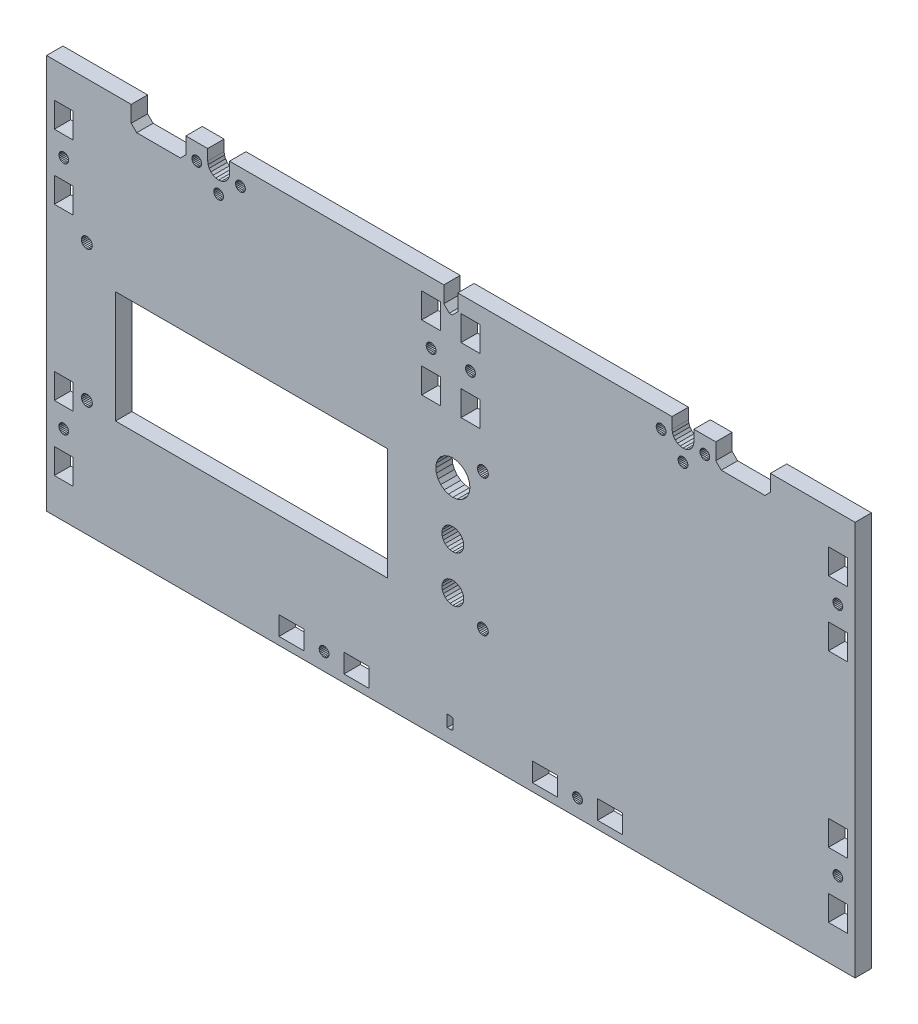
SolidWorks part; units mm, degrees
material "Maple"
ref_plane "Front Plane" through (0, 0, 0) normal (0, 0, 1) x (1, 0, 0)
ref_plane "Top Plane" through (0, 0, 0) normal (0, 1, 0) x (1, 0, 0)
ref_plane "Right Plane" through (0, 0, 0) normal (1, 0, 0) x (0, 0, -1)
sketch "Sketch1" plane through (0, 0, 0) normal (0, 0, 1) x (1, 0, 0)
  line L5557 (-18.0811, -260.3965) -> (-17.9448, -259.3613)
  line L5558 (-189.9448, -262.8254) -> (-189.1163, -262.1897)
  line L5559 (-21.9448, -263.3613) -> (-20.9095, -263.225)
  line L5560 (41.0552, -255.3613) -> (41.0552, -399.8612)
  line L5561 (-254.9447, -255.3613) -> (-223.9448, -255.3613)
  line L5562 (8.0552, -263.3613) -> (-7.9448, -263.3613)
  line L5563 (-9.9448, -255.3613) -> (-9.9448, -261.3613)
  line L5564 (-189.1163, -262.1897) -> (-188.4807, -261.3613)
  line L5565 (-19.1164, -262.1897) -> (-18.4807, -261.3613)
  line L5566 (-223.9448, -261.3613) -> (-223.9448, -255.3613)
  line L5567 (-20.9095, -263.225) -> (-19.9448, -262.8254)
  line L5568 (-25.9448, -259.3613) -> (-25.8085, -260.3965)
  line L5569 (-188.0811, -260.3965) -> (-187.9448, -259.3613)
  line L5570 (-203.9448, -255.3613) -> (-195.9448, -255.3613)
  line L5571 (-188.4807, -261.3613) -> (-188.0811, -260.3965)
  line L5572 (-223.9448, -261.3613) -> (-221.9448, -263.3613)
  line L5573 (-203.9448, -261.3613) -> (-203.9448, -255.3613)
  line L5574 (-193.9448, -262.8254) -> (-192.98, -263.225)
  line L5575 (10.0552, -255.3613) -> (10.0552, -261.3613)
  line L5576 (-187.9448, -255.3613) -> (-109.4948, -255.3613)
  line L5577 (-195.9448, -259.3613) -> (-195.8085, -260.3965)
  line L5578 (-17.9448, -259.3613) -> (-17.9448, -255.3613)
  line L5579 (-192.98, -263.225) -> (-191.9448, -263.3613)
  line L5580 (-205.9448, -263.3613) -> (-221.9448, -263.3613)
  line L5581 (-9.9448, -261.3613) -> (-7.9448, -263.3613)
  line L5582 (-17.9448, -255.3613) -> (-9.9448, -255.3613)
  line L5583 (-23.9448, -262.8254) -> (-22.9801, -263.225)
  line L5584 (-25.4089, -261.3613) -> (-24.7732, -262.1897)
  line L5585 (41.0552, -399.8612) -> (-254.9447, -399.8612)
  line L5586 (-18.4807, -261.3613) -> (-18.0811, -260.3965)
  line L5587 (-195.9448, -259.3613) -> (-195.9448, -255.3613)
  line L5588 (-195.8085, -260.3965) -> (-195.4089, -261.3613)
  line L5589 (-19.9448, -262.8254) -> (-19.1164, -262.1897)
  line L5590 (-254.9447, -399.8612) -> (-254.9447, -255.3613)
  line L5591 (10.0552, -261.3613) -> (8.0552, -263.3613)
  line L5592 (-25.8085, -260.3965) -> (-25.4089, -261.3613)
  line L5593 (-22.9801, -263.225) -> (-21.9448, -263.3613)
  line L5594 (-187.9448, -259.3613) -> (-187.9448, -255.3613)
  line L5595 (-191.9448, -263.3613) -> (-190.9095, -263.225)
  line L5596 (-195.4089, -261.3613) -> (-194.7732, -262.1897)
  line L5597 (-25.9448, -259.3613) -> (-25.9448, -255.3613)
  line L5598 (10.0552, -255.3613) -> (41.0552, -255.3613)
  line L5599 (-203.9448, -261.3613) -> (-205.9448, -263.3613)
  line L5600 (-190.9095, -263.225) -> (-189.9448, -262.8254)
  line L5601 (-24.7732, -262.1897) -> (-23.9448, -262.8254)
  line L5602 (-194.7732, -262.1897) -> (-193.9448, -262.8254)
  line L5603 (36.0292, -285.7853) -> (36.3155, -285.4121)
  line L5604 (-190.3859, -266.9613) -> (-190.672, -266.5885)
  line L5605 (-13.4801, -259.6226) -> (-13.9459, -259.5613)
  line L5606 (-185.6846, -260.8954) -> (-185.7459, -261.3613)
  line L5607 (38.2052, -268.0113) -> (31.3052, -268.0113)
  line L5608 (-252.0947, -301.1113) -> (-245.1947, -301.1113)
  line L5609 (-190.3859, -268.7613) -> (-190.2061, -268.3271)
  line L5610 (35.656, -282.9509) -> (35.2215, -282.7709)
  line L5611 (-198.1448, -261.3613) -> (-198.2061, -260.8954)
  line L5612 (33.4811, -283.2372) -> (33.1948, -283.6104)
  line L5613 (-59.2708, -394.8353) -> (-58.9845, -394.4621)
  line L5614 (-62.3465, -393.5613) -> (-62.2851, -394.0276)
  line L5615 (-30.8448, -262.9201) -> (-30.4107, -263.0999)
  line L5616 (-30.4107, -259.6226) -> (-30.8448, -259.8024)
  line L5617 (-185.2187, -260.0885) -> (-185.5047, -260.4613)
  line L5618 (-198.3859, -260.4613) -> (-198.672, -260.0885)
  line L5619 (-182.2072, -260.8954) -> (-182.387, -260.4613)
  line L5620 (-252.0947, -268.1113) -> (-252.0947, -277.3113)
  line L5621 (-31.7448, -261.3613) -> (-31.6835, -261.8271)
  line L5622 (-67.8448, -397.0113) -> (-67.8448, -390.1112)
  line L5623 (-154.9051, -394.4621) -> (-154.6188, -394.8353)
  line L5624 (-192.4106, -269.5999) -> (-191.9448, -269.6613)
  line L5625 (-246.9044, -285.0776) -> (-246.843, -284.6113)
  line L5626 (-160.6448, -390.1112) -> (-169.8448, -390.1112)
  line L5627 (-247.7439, -286.1716) -> (-247.3707, -285.8853)
  line L5628 (-192.4106, -266.1226) -> (-192.8448, -266.3024)
  line L5629 (31.3052, -301.0113) -> (38.2052, -301.0113)
  line L5630 (-136.8448, -397.0113) -> (-136.8448, -390.1112)
  line L5631 (-23.2176, -269.1341) -> (-22.8448, -269.4201)
  line L5632 (-183.9459, -263.1613) -> (-183.48, -263.0999)
  line L5633 (-252.0947, -291.9113) -> (-252.0947, -301.1113)
  line L5634 (-155.0851, -393.0949) -> (-155.1465, -393.5613)
  line L5635 (-250.3851, -285.0776) -> (-250.2051, -285.5121)
  line L5636 (-183.9459, -259.5613) -> (-184.4118, -259.6226)
  line L5637 (33.0148, -284.0449) -> (32.9534, -284.5113)
  line L5638 (-182.6731, -260.0885) -> (-183.0459, -259.8024)
  line L5639 (-15.6846, -260.8954) -> (-15.7459, -261.3613)
  line L5640 (-247.0844, -283.7104) -> (-247.3707, -283.3372)
  line L5641 (-29.0448, -262.9201) -> (-28.672, -262.6341)
  line L5642 (-29.4789, -259.6226) -> (-29.9448, -259.5613)
  line L5643 (-146.0448, -390.1112) -> (-146.0448, -397.0113)
  line L5644 (-61.8188, -392.2872) -> (-62.1052, -392.6604)
  line L5645 (-61.0111, -395.3016) -> (-60.5448, -395.363)
  line L5646 (-61.4457, -395.1216) -> (-61.0111, -395.3016)
  line L5647 (-250.2051, -285.5121) -> (-249.9188, -285.8853)
  line L5648 (-20.2062, -268.3271) -> (-20.1448, -267.8613)
  line L5649 (-193.6834, -267.3954) -> (-193.7448, -267.8613)
  line L5650 (-249.9188, -285.8853) -> (-249.5456, -286.1716)
  line L5651 (-28.2062, -261.8271) -> (-28.1448, -261.3613)
  line L5652 (-151.7844, -392.6604) -> (-152.0708, -392.2872)
  line L5653 (-199.9448, -259.5613) -> (-200.4106, -259.6226)
  line L5654 (-12.6731, -262.6341) -> (-12.3871, -262.2613)
  line L5655 (-31.2176, -262.6341) -> (-30.8448, -262.9201)
  line L5656 (-191.0448, -266.3024) -> (-191.4789, -266.1226)
  line L5657 (-199.9448, -263.1613) -> (-199.4789, -263.0999)
  line L5658 (31.3052, -268.0113) -> (31.3052, -277.2113)
  line L5659 (-190.672, -266.5885) -> (-191.0448, -266.3024)
  line L5660 (-152.4439, -395.1216) -> (-152.0708, -394.8353)
  line L5661 (-15.5048, -262.2613) -> (-15.2187, -262.6341)
  line L5662 (-12.3871, -260.4613) -> (-12.6731, -260.0885)
  line L5663 (-28.672, -262.6341) -> (-28.386, -262.2613)
  line L5664 (-20.386, -266.9613) -> (-20.672, -266.5885)
  line L5665 (-252.0947, -277.3113) -> (-245.1947, -277.3113)
  line L5666 (-23.5037, -266.9613) -> (-23.6835, -267.3954)
  line L5667 (32.9534, -284.5113) -> (33.0148, -284.9776)
  line L5668 (-182.387, -262.2613) -> (-182.2072, -261.8271)
  line L5669 (-201.2176, -262.6341) -> (-200.8448, -262.9201)
  line L5670 (-20.672, -269.1341) -> (-20.386, -268.7613)
  line L5671 (-136.8448, -390.1112) -> (-146.0448, -390.1112)
  line L5672 (-151.7844, -394.4621) -> (-151.6044, -394.0276)
  line L5673 (-20.672, -266.5885) -> (-21.0448, -266.3024)
  line L5674 (-14.8459, -259.8024) -> (-15.2187, -260.0885)
  line L5675 (-198.672, -260.0885) -> (-199.0448, -259.8024)
  line L5676 (-13.4801, -263.0999) -> (-13.0459, -262.9201)
  line L5677 (36.4955, -284.9776) -> (36.5569, -284.5113)
  line L5678 (33.0148, -284.9776) -> (33.1948, -285.4121)
  line L5679 (-23.5037, -268.7613) -> (-23.2176, -269.1341)
  line L5680 (-151.6044, -394.0276) -> (-151.5431, -393.5613)
  line L5681 (-185.5047, -262.2613) -> (-185.2187, -262.6341)
  line L5682 (-183.0459, -262.9201) -> (-182.6731, -262.6341)
  line L5683 (-146.0448, -397.0113) -> (-136.8448, -397.0113)
  line L5684 (-192.8448, -269.4201) -> (-192.4106, -269.5999)
  line L5685 (33.8543, -286.0716) -> (34.2888, -286.2516)
  line L5686 (34.7552, -282.7095) -> (34.2888, -282.7709)
  line L5687 (-191.9448, -266.0613) -> (-192.4106, -266.1226)
  line L5688 (-14.4118, -263.0999) -> (-13.9459, -263.1613)
  line L5689 (-184.8459, -259.8024) -> (-185.2187, -260.0885)
  line L5690 (-21.9448, -266.0613) -> (-22.4107, -266.1226)
  line L5691 (-21.9448, -269.6613) -> (-21.4789, -269.5999)
  line L5692 (-22.8448, -269.4201) -> (-22.4107, -269.5999)
  line L5693 (-23.7448, -267.8613) -> (-23.6835, -268.3271)
  line L5694 (-22.8448, -266.3024) -> (-23.2176, -266.5885)
  line L5695 (-200.4106, -263.0999) -> (-199.9448, -263.1613)
  line L5696 (-154.6188, -394.8353) -> (-154.2456, -395.1216)
  line L5697 (-153.3448, -391.7595) -> (-153.8111, -391.8209)
  line L5698 (-152.8785, -391.8209) -> (-153.3448, -391.7595)
  line L5699 (-152.0708, -392.2872) -> (-152.4439, -392.0009)
  line L5700 (-60.0785, -395.3016) -> (-59.644, -395.1216)
  line L5701 (-62.2851, -394.0276) -> (-62.1052, -394.4621)
  line L5702 (-61.0111, -391.8209) -> (-61.4457, -392.0009)
  line L5703 (-29.0448, -259.8024) -> (-29.4789, -259.6226)
  line L5704 (-249.1111, -282.8709) -> (-249.5456, -283.0509)
  line L5705 (36.3155, -369.7104) -> (36.0292, -369.3372)
  line L5706 (33.1948, -371.5121) -> (33.4811, -371.8853)
  line L5707 (31.3052, -363.3113) -> (38.2052, -363.3113)
  line L5708 (36.0292, -371.8853) -> (36.3155, -371.5121)
  line L5709 (34.7552, -368.8095) -> (34.2888, -368.8709)
  line L5710 (35.656, -372.1716) -> (36.0292, -371.8853)
  line L5711 (35.656, -369.0509) -> (35.2215, -368.8709)
  line L5712 (36.5569, -370.6113) -> (36.4955, -370.1449)
  line L5713 (34.2888, -368.8709) -> (33.8543, -369.0509)
  line L5714 (36.3155, -371.5121) -> (36.4955, -371.0776)
  line L5715 (38.2052, -377.9113) -> (31.3052, -377.9113)
  line L5716 (32.9534, -370.6113) -> (33.0148, -371.0776)
  line L5717 (35.2215, -372.3516) -> (35.656, -372.1716)
  line L5718 (34.2888, -372.3516) -> (34.7552, -372.413)
  line L5719 (-249.5456, -372.1716) -> (-249.1111, -372.3516)
  line L5720 (-247.7439, -369.0509) -> (-248.1784, -368.8709)
  line L5721 (-245.1947, -354.1113) -> (-252.0947, -354.1113)
  line L5722 (-250.3851, -371.0776) -> (-250.2051, -371.5121)
  line L5723 (-249.5456, -369.0509) -> (-249.9188, -369.3372)
  line L5724 (-250.4465, -370.6113) -> (-250.3851, -371.0776)
  line L5725 (-247.3707, -371.8853) -> (-247.0844, -371.5121)
  line L5726 (-247.0844, -371.5121) -> (-246.9044, -371.0776)
  line L5727 (-246.9044, -370.1449) -> (-247.0844, -369.7104)
  line L5728 (-246.9044, -371.0776) -> (-246.843, -370.6113)
  line L5729 (-248.1784, -368.8709) -> (-248.6447, -368.8095)
  line L5730 (-249.9188, -371.8853) -> (-249.5456, -372.1716)
  line L5731 (-250.2051, -371.5121) -> (-249.9188, -371.8853)
  line L5732 (-249.1111, -372.3516) -> (-248.6447, -372.413)
  line L5733 (-252.0947, -387.1112) -> (-245.1947, -387.1112)
  line L5734 (-247.7439, -372.1716) -> (-247.3707, -371.8853)
  line L5735 (-102.3378, -333.3081) -> (-102.7374, -332.3433)
  line L5736 (-110.0652, -333.3081) -> (-110.2015, -334.3433)
  line L5737 (-108.2015, -330.8792) -> (-109.0299, -331.5149)
  line L5738 (-109.6656, -353.3433) -> (-109.0299, -354.1718)
  line L5739 (-107.2367, -330.4796) -> (-108.2015, -330.8792)
  line L5740 (-110.2015, -351.3433) -> (-110.0652, -352.3786)
  line L5741 (-109.6656, -332.3433) -> (-110.0652, -333.3081)
  line L5742 (-103.0765, -309.4307) -> (-104.5838, -308.8063)
  line L5743 (-110.6209, -319.2627) -> (-109.3265, -320.256)
  line L5744 (-102.3378, -350.308) -> (-102.7374, -349.3433)
  line L5745 (-102.2015, -351.3433) -> (-102.3378, -350.308)
  line L5746 (-112.4515, -314.8433) -> (-112.2385, -316.4609)
  line L5747 (-104.2015, -354.8074) -> (-103.373, -354.1718)
  line L5748 (-109.3265, -309.4307) -> (-110.6209, -310.4239)
  line L5749 (-107.2367, -355.207) -> (-106.2015, -355.3433)
  line L5750 (-99.9515, -314.8433) -> (-100.1644, -313.2257)
  line L5751 (-104.2015, -330.8792) -> (-105.1662, -330.4796)
  line L5752 (-102.3378, -335.3786) -> (-102.2015, -334.3433)
  line L5753 (-111.6141, -311.7183) -> (-112.2385, -313.2257)
  line L5754 (-109.6656, -336.3433) -> (-109.0299, -337.1718)
  line L5755 (-112.2385, -313.2257) -> (-112.4515, -314.8433)
  line L5756 (-110.0652, -350.308) -> (-110.2015, -351.3433)
  line L5757 (-229.7014, -358.6433) -> (-130.2015, -358.6433)
  line L5758 (-108.2015, -337.8074) -> (-107.2367, -338.207)
  line L5759 (-101.782, -319.2627) -> (-100.7888, -317.9683)
  line L5760 (-107.8191, -308.8063) -> (-109.3265, -309.4307)
  line L5761 (-229.7014, -317.6433) -> (-229.7014, -358.6433)
  line L5762 (-106.2015, -355.3433) -> (-105.1662, -355.207)
  line L5763 (-109.6656, -349.3433) -> (-110.0652, -350.308)
  line L5764 (-102.7374, -336.3433) -> (-102.3378, -335.3786)
  line L5765 (-103.373, -337.1718) -> (-102.7374, -336.3433)
  line L5766 (-107.2367, -338.207) -> (-106.2015, -338.3433)
  line L5767 (33.1948, -369.7104) -> (33.0148, -370.1449)
  line L5768 (-14.8459, -262.9201) -> (-14.4118, -263.0999)
  line L5769 (-28.1448, -261.3613) -> (-28.2062, -260.8954)
  line L5770 (33.8543, -372.1716) -> (34.2888, -372.3516)
  line L5771 (-108.2015, -354.8074) -> (-107.2367, -355.207)
  line L5772 (-112.2385, -316.4609) -> (-111.6141, -317.9683)
  line L5773 (-152.4439, -392.0009) -> (-152.8785, -391.8209)
  line L5774 (38.2052, -387.1112) -> (38.2052, -377.9113)
  line L5775 (-250.3851, -284.1449) -> (-250.4465, -284.6113)
  line L5776 (-247.0844, -369.7104) -> (-247.3707, -369.3372)
  line L5777 (-200.4106, -259.6226) -> (-200.8448, -259.8024)
  line L5778 (-100.7888, -317.9683) -> (-100.1644, -316.4609)
  line L5779 (-106.2203, -394.8434) -> (-106.1594, -394.7541)
  line L5780 (-106.1594, -394.7541) -> (-106.1391, -394.6577)
  line L5781 (-199.0448, -262.9201) -> (-198.672, -262.6341)
  line L5782 (-110.2015, -334.3433) -> (-110.0652, -335.3786)
  line L5783 (-109.3265, -320.256) -> (-107.8191, -320.8804)
  line L5784 (33.1948, -285.4121) -> (33.4811, -285.7853)
  line L5785 (-193.2176, -266.5885) -> (-193.5036, -266.9613)
  line L5786 (-190.672, -269.1341) -> (-190.3859, -268.7613)
  line L5787 (-155.1465, -393.5613) -> (-155.0851, -394.0276)
  line L5788 (34.7552, -372.413) -> (35.2215, -372.3516)
  line L5789 (31.3052, -277.2113) -> (38.2052, -277.2113)
  line L5790 (-67.8448, -390.1112) -> (-77.0448, -390.1112)
  line L5791 (-21.0448, -269.4201) -> (-20.672, -269.1341)
  line L5792 (-20.1448, -267.8613) -> (-20.2062, -267.3954)
  line L5793 (-103.373, -348.5149) -> (-104.2015, -347.8792)
  line L5794 (-31.2176, -260.0885) -> (-31.5037, -260.4613)
  line L5795 (-23.6835, -268.3271) -> (-23.5037, -268.7613)
  line L5796 (-106.2015, -347.3433) -> (-107.2367, -347.4796)
  line L5797 (36.3155, -283.6104) -> (36.0292, -283.2372)
  line L5798 (35.2215, -286.2516) -> (35.656, -286.0716)
  line L5799 (-248.6447, -372.413) -> (-248.1784, -372.3516)
  line L5800 (-31.5037, -262.2613) -> (-31.2176, -262.6341)
  line L5801 (-106.8291, -390.8664) -> (-107.263, -390.8305)
  line L5802 (-105.1662, -347.4796) -> (-106.2015, -347.3433)
  line L5803 (-183.48, -263.0999) -> (-183.0459, -262.9201)
  line L5804 (-193.7448, -267.8613) -> (-193.6834, -268.3271)
  line L5805 (-59.644, -395.1216) -> (-59.2708, -394.8353)
  line L5806 (-152.0708, -394.8353) -> (-151.7844, -394.4621)
  line L5807 (34.2888, -286.2516) -> (34.7552, -286.313)
  line L5808 (-62.2851, -393.0949) -> (-62.3465, -393.5613)
  line L5809 (-250.4465, -284.6113) -> (-250.3851, -285.0776)
  line L5810 (33.4811, -371.8853) -> (33.8543, -372.1716)
  line L5811 (-247.3707, -283.3372) -> (-247.7439, -283.0509)
  line L5812 (-153.8111, -391.8209) -> (-154.2456, -392.0009)
  line L5813 (-44.0448, -397.0113) -> (-44.0448, -390.1112)
  line L5814 (31.3052, -377.9113) -> (31.3052, -387.1112)
  line L5815 (-185.5047, -260.4613) -> (-185.6846, -260.8954)
  line L5816 (36.4955, -284.0449) -> (36.3155, -283.6104)
  line L5817 (-246.843, -284.6113) -> (-246.9044, -284.1449)
  line L5818 (38.2052, -277.2113) -> (38.2052, -268.0113)
  line L5819 (-28.386, -260.4613) -> (-28.672, -260.0885)
  line L5820 (-182.387, -260.4613) -> (-182.6731, -260.0885)
  line L5821 (-60.5448, -395.363) -> (-60.0785, -395.3016)
  line L5822 (-106.1594, -391.2176) -> (-106.2203, -391.1302)
  line L5823 (-183.0459, -259.8024) -> (-183.48, -259.6226)
  line L5824 (-44.0448, -390.1112) -> (-53.2448, -390.1112)
  line L5825 (-245.1947, -363.3113) -> (-245.1947, -354.1113)
  line L5826 (-23.6835, -267.3954) -> (-23.7448, -267.8613)
  line L5827 (-106.2015, -308.5933) -> (-107.8191, -308.8063)
  line L5828 (-151.6044, -393.0949) -> (-151.7844, -392.6604)
  line L5829 (-30.4107, -263.0999) -> (-29.9448, -263.1613)
  line L5830 (-106.2015, -321.0933) -> (-104.5838, -320.8804)
  line L5831 (-22.4107, -269.5999) -> (-21.9448, -269.6613)
  line L5832 (-153.8111, -395.3016) -> (-153.3448, -395.363)
  line L5833 (36.5569, -284.5113) -> (36.4955, -284.0449)
  line L5834 (-252.0947, -377.9113) -> (-252.0947, -387.1112)
  line L5835 (-101.782, -310.4239) -> (-103.0765, -309.4307)
  line L5836 (-29.4789, -263.0999) -> (-29.0448, -262.9201)
  line L5837 (-110.0652, -335.3786) -> (-109.6656, -336.3433)
  line L5838 (-29.9448, -263.1613) -> (-29.4789, -263.0999)
  line L5839 (-15.6846, -261.8271) -> (-15.5048, -262.2613)
  line L5840 (-182.2072, -261.8271) -> (-182.1459, -261.3613)
  line L5841 (38.2052, -354.1113) -> (31.3052, -354.1113)
  line L5842 (-198.2061, -260.8954) -> (-198.3859, -260.4613)
  line L5843 (-252.0947, -354.1113) -> (-252.0947, -363.3113)
  line L5844 (-13.0459, -259.8024) -> (-13.4801, -259.6226)
  line L5845 (-191.9448, -269.6613) -> (-191.4789, -269.5999)
  line L5846 (-108.2808, -390.8305) -> (-107.263, -390.8305)
  line L5847 (-250.3851, -370.1449) -> (-250.4465, -370.6113)
  line L5848 (-185.2187, -262.6341) -> (-184.8459, -262.9201)
  line L5849 (-246.843, -370.6113) -> (-246.9044, -370.1449)
  line L5850 (-77.0448, -390.1112) -> (-77.0448, -397.0113)
  line L5851 (-199.0448, -259.8024) -> (-199.4789, -259.6226)
  line L5852 (-20.2062, -267.3954) -> (-20.386, -266.9613)
  line L5853 (-102.2015, -334.3433) -> (-102.3378, -333.3081)
  line L5854 (-182.1459, -261.3613) -> (-182.2072, -260.8954)
  line L5855 (-106.2015, -338.3433) -> (-105.1662, -338.207)
  line L5856 (36.4955, -371.0776) -> (36.5569, -370.6113)
  line L5857 (35.656, -286.0716) -> (36.0292, -285.7853)
  line L5858 (38.2052, -291.8113) -> (31.3052, -291.8113)
  line L5859 (-104.2015, -337.8074) -> (-103.373, -337.1718)
  line L5860 (-31.6835, -261.8271) -> (-31.5037, -262.2613)
  line L5861 (33.4811, -285.7853) -> (33.8543, -286.0716)
  line L5862 (-193.2176, -269.1341) -> (-192.8448, -269.4201)
  line L5863 (-248.1784, -282.8709) -> (-248.6447, -282.8095)
  line L5864 (-31.6835, -260.8954) -> (-31.7448, -261.3613)
  line L5865 (33.8543, -369.0509) -> (33.4811, -369.3372)
  line L5866 (-247.3707, -369.3372) -> (-247.7439, -369.0509)
  line L5867 (-249.1111, -286.3516) -> (-248.6447, -286.413)
  line L5868 (-198.3859, -262.2613) -> (-198.2061, -261.8271)
  line L5869 (-13.9459, -263.1613) -> (-13.4801, -263.0999)
  line L5870 (-248.6447, -282.8095) -> (-249.1111, -282.8709)
  line L5871 (-200.8448, -259.8024) -> (-201.2176, -260.0885)
  line L5872 (-154.2456, -395.1216) -> (-153.8111, -395.3016)
  line L5873 (-169.8448, -397.0113) -> (-160.6448, -397.0113)
  line L5874 (-248.1784, -286.3516) -> (-247.7439, -286.1716)
  line L5875 (-12.2073, -261.8271) -> (-12.1459, -261.3613)
  line L5876 (-153.3448, -395.363) -> (-152.8785, -395.3016)
  line L5877 (-190.2061, -268.3271) -> (-190.1448, -267.8613)
  line L5878 (-58.9845, -392.6604) -> (-59.2708, -392.2872)
  line L5879 (-61.4457, -392.0009) -> (-61.8188, -392.2872)
  line L5880 (-193.5036, -268.7613) -> (-193.2176, -269.1341)
  line L5881 (31.3052, -354.1113) -> (31.3052, -363.3113)
  line L5882 (-248.6447, -368.8095) -> (-249.1111, -368.8709)
  line L5883 (-201.2176, -260.0885) -> (-201.5036, -260.4613)
  line L5884 (-100.7888, -311.7183) -> (-101.782, -310.4239)
  line L5885 (-60.5448, -391.7595) -> (-61.0111, -391.8209)
  line L5886 (-102.7374, -332.3433) -> (-103.373, -331.5149)
  line L5887 (-15.5048, -260.4613) -> (-15.6846, -260.8954)
  line L5888 (-105.1662, -338.207) -> (-104.2015, -337.8074)
  line L5889 (33.4811, -369.3372) -> (33.1948, -369.7104)
  line L5890 (35.2215, -282.7709) -> (34.7552, -282.7095)
  line L5891 (-250.2051, -369.7104) -> (-250.3851, -370.1449)
  line L5892 (-15.2187, -262.6341) -> (-14.8459, -262.9201)
  line L5893 (-184.4118, -263.0999) -> (-183.9459, -263.1613)
  line L5894 (-201.5036, -262.2613) -> (-201.2176, -262.6341)
  line L5895 (-245.1947, -301.1113) -> (-245.1947, -291.9113)
  line L5896 (-58.8045, -393.0949) -> (-58.9845, -392.6604)
  line L5897 (-185.7459, -261.3613) -> (-185.6846, -261.8271)
  line L5898 (-249.5456, -286.1716) -> (-249.1111, -286.3516)
  line L5899 (-154.2456, -392.0009) -> (-154.6188, -392.2872)
  line L5900 (-201.6834, -261.8271) -> (-201.5036, -262.2613)
  line L5901 (-28.386, -262.2613) -> (-28.2062, -261.8271)
  line L5902 (-152.8785, -395.3016) -> (-152.4439, -395.1216)
  line L5903 (-245.1947, -291.9113) -> (-252.0947, -291.9113)
  line L5904 (-12.6731, -260.0885) -> (-13.0459, -259.8024)
  line L5905 (-249.9188, -283.3372) -> (-250.2051, -283.7104)
  line L5906 (-53.2448, -390.1112) -> (-53.2448, -397.0113)
  line L5907 (-109.0299, -348.5149) -> (-109.6656, -349.3433)
  line L5908 (-106.4638, -395.0011) -> (-106.8197, -395.1041)
  line L5909 (-106.8197, -395.1041) -> (-107.263, -395.1384)
  line L5910 (-109.0299, -354.1718) -> (-108.2015, -354.8074)
  line L5911 (-182.6731, -262.6341) -> (-182.387, -262.2613)
  line L5912 (-104.5838, -308.8063) -> (-106.2015, -308.5933)
  line L5913 (36.3155, -285.4121) -> (36.4955, -284.9776)
  line L5914 (-102.7374, -353.3433) -> (-102.3378, -352.3786)
  line L5915 (-12.1459, -261.3613) -> (-12.2073, -260.8954)
  line L5916 (-58.8045, -394.0276) -> (-58.7431, -393.5613)
  line L5917 (-245.1947, -277.3113) -> (-245.1947, -268.1113)
  line L5918 (-13.0459, -262.9201) -> (-12.6731, -262.6341)
  line L5919 (-23.2176, -266.5885) -> (-23.5037, -266.9613)
  line L5920 (-100.1644, -316.4609) -> (-99.9515, -314.8433)
  line L5921 (-169.8448, -390.1112) -> (-169.8448, -397.0113)
  line L5922 (-53.2448, -397.0113) -> (-44.0448, -397.0113)
  line L5923 (-12.3871, -262.2613) -> (-12.2073, -261.8271)
  line L5924 (-245.1947, -387.1112) -> (-245.1947, -377.9113)
  line L5925 (-59.644, -392.0009) -> (-60.0785, -391.8209)
  line L5926 (-191.0448, -269.4201) -> (-190.672, -269.1341)
  line L5927 (-201.6834, -260.8954) -> (-201.7448, -261.3613)
  line L5928 (-107.8191, -320.8804) -> (-106.2015, -321.0933)
  line L5929 (-245.1947, -377.9113) -> (-252.0947, -377.9113)
  line L5930 (-247.7439, -283.0509) -> (-248.1784, -282.8709)
  line L5931 (33.8543, -282.9509) -> (33.4811, -283.2372)
  line L5932 (-110.0652, -352.3786) -> (-109.6656, -353.3433)
  line L5933 (-106.2015, -330.3433) -> (-107.2367, -330.4796)
  line L5934 (38.2052, -301.0113) -> (38.2052, -291.8113)
  line L5935 (-15.7459, -261.3613) -> (-15.6846, -261.8271)
  line L5936 (-190.2061, -267.3954) -> (-190.3859, -266.9613)
  line L5937 (-28.672, -260.0885) -> (-29.0448, -259.8024)
  line L5938 (33.0148, -370.1449) -> (32.9534, -370.6113)
  line L5939 (-103.373, -331.5149) -> (-104.2015, -330.8792)
  line L5940 (-247.3707, -285.8853) -> (-247.0844, -285.5121)
  line L5941 (-200.8448, -262.9201) -> (-200.4106, -263.0999)
  line L5942 (-252.0947, -363.3113) -> (-245.1947, -363.3113)
  line L5943 (-106.1391, -391.3113) -> (-106.1391, -394.6577)
  line L5944 (-29.9448, -259.5613) -> (-30.4107, -259.6226)
  line L5945 (-62.1052, -392.6604) -> (-62.2851, -393.0949)
  line L5946 (-14.4118, -259.6226) -> (-14.8459, -259.8024)
  line L5947 (-102.7374, -349.3433) -> (-103.373, -348.5149)
  line L5948 (-21.4789, -266.1226) -> (-21.9448, -266.0613)
  line L5949 (-109.0299, -331.5149) -> (-109.6656, -332.3433)
  line L5950 (34.2888, -282.7709) -> (33.8543, -282.9509)
  line L5951 (-22.4107, -266.1226) -> (-22.8448, -266.3024)
  line L5952 (-21.0448, -266.3024) -> (-21.4789, -266.1226)
  line L5953 (-201.7448, -261.3613) -> (-201.6834, -261.8271)
  line L5954 (36.4955, -370.1449) -> (36.3155, -369.7104)
  line L5955 (-21.4789, -269.5999) -> (-21.0448, -269.4201)
  line L5956 (-12.2073, -260.8954) -> (-12.3871, -260.4613)
  line L5957 (31.3052, -291.8113) -> (31.3052, -301.0113)
  line L5958 (-198.2061, -261.8271) -> (-198.1448, -261.3613)
  line L5959 (34.7552, -286.313) -> (35.2215, -286.2516)
  line L5960 (-103.0765, -320.256) -> (-101.782, -319.2627)
  line L5961 (-184.4118, -259.6226) -> (-184.8459, -259.8024)
  line L5962 (-249.9188, -369.3372) -> (-250.2051, -369.7104)
  line L5963 (-249.5456, -283.0509) -> (-249.9188, -283.3372)
  line L5964 (-246.9044, -284.1449) -> (-247.0844, -283.7104)
  line L5965 (-104.2015, -347.8792) -> (-105.1662, -347.4796)
  line L5966 (-154.6188, -392.2872) -> (-154.9051, -392.6604)
  line L5967 (-28.2062, -260.8954) -> (-28.386, -260.4613)
  line L5968 (-248.1784, -372.3516) -> (-247.7439, -372.1716)
  line L5969 (36.0292, -369.3372) -> (35.656, -369.0509)
  line L5970 (-191.4789, -266.1226) -> (-191.9448, -266.0613)
  line L5971 (-190.1448, -267.8613) -> (-190.2061, -267.3954)
  line L5972 (-58.7431, -393.5613) -> (-58.8045, -393.0949)
  line L5973 (-199.4789, -259.6226) -> (-199.9448, -259.5613)
  line L5974 (-62.1052, -394.4621) -> (-61.8188, -394.8353)
  line L5975 (-77.0448, -397.0113) -> (-67.8448, -397.0113)
  line L5976 (31.3052, -387.1112) -> (38.2052, -387.1112)
  line L5977 (-250.2051, -283.7104) -> (-250.3851, -284.1449)
  line L5978 (-105.1662, -330.4796) -> (-106.2015, -330.3433)
  line L5979 (-31.5037, -260.4613) -> (-31.6835, -260.8954)
  line L5980 (-184.8459, -262.9201) -> (-184.4118, -263.0999)
  line L5981 (-110.6209, -310.4239) -> (-111.6141, -311.7183)
  line L5982 (-248.6447, -286.413) -> (-248.1784, -286.3516)
  line L5983 (-130.2015, -317.6433) -> (-229.7014, -317.6433)
  line L5984 (-249.1111, -368.8709) -> (-249.5456, -369.0509)
  line L5985 (-109.0299, -337.1718) -> (-108.2015, -337.8074)
  line L5986 (-104.5838, -320.8804) -> (-103.0765, -320.256)
  line L5987 (-13.9459, -259.5613) -> (-14.4118, -259.6226)
  line L5988 (-183.48, -259.6226) -> (-183.9459, -259.5613)
  line L5989 (33.0148, -371.0776) -> (33.1948, -371.5121)
  line L5990 (-106.8291, -390.8664) -> (-106.4638, -390.9741)
  line L5991 (-106.4638, -390.9741) -> (-106.2203, -391.1302)
  line L5992 (-58.9845, -394.4621) -> (-58.8045, -394.0276)
  line L5993 (-59.2708, -392.2872) -> (-59.644, -392.0009)
  line L5994 (-199.4789, -263.0999) -> (-199.0448, -262.9201)
  line L5995 (-151.5431, -393.5613) -> (-151.6044, -393.0949)
  line L5996 (-105.1662, -355.207) -> (-104.2015, -354.8074)
  line L5997 (-130.2015, -358.6433) -> (-130.2015, -317.6433)
  line L5998 (-247.0844, -285.5121) -> (-246.9044, -285.0776)
  line L5999 (-103.373, -354.1718) -> (-102.7374, -353.3433)
  line L6000 (36.0292, -283.2372) -> (35.656, -282.9509)
  line L6001 (-61.8188, -394.8353) -> (-61.4457, -395.1216)
  line L6002 (-160.6448, -397.0113) -> (-160.6448, -390.1112)
  line L6003 (-193.6834, -268.3271) -> (-193.5036, -268.7613)
  line L6004 (-193.5036, -266.9613) -> (-193.6834, -267.3954)
  line L6005 (-20.386, -268.7613) -> (-20.2062, -268.3271)
  line L6006 (-191.4789, -269.5999) -> (-191.0448, -269.4201)
  line L6007 (-108.2808, -395.1384) -> (-108.2808, -390.8305)
  line L6008 (-107.2367, -347.4796) -> (-108.2015, -347.8792)
  line L6009 (-198.672, -262.6341) -> (-198.3859, -262.2613)
  line L6010 (-60.0785, -391.8209) -> (-60.5448, -391.7595)
  line L6011 (-245.1947, -268.1113) -> (-252.0947, -268.1113)
  line L6012 (-106.1391, -391.3113) -> (-106.1594, -391.2176)
  line L6013 (-154.9051, -392.6604) -> (-155.0851, -393.0949)
  line L6014 (-155.0851, -394.0276) -> (-154.9051, -394.4621)
  line L6015 (-106.4638, -395.0011) -> (-106.2203, -394.8434)
  line L6016 (-100.1644, -313.2257) -> (-100.7888, -311.7183)
  line L6017 (-108.2015, -347.8792) -> (-109.0299, -348.5149)
  line L6018 (-185.6846, -261.8271) -> (-185.5047, -262.2613)
  line L6019 (-111.6141, -317.9683) -> (-110.6209, -319.2627)
  line L6020 (-108.2808, -395.1384) -> (-107.263, -395.1384)
  line L6021 (38.2052, -363.3113) -> (38.2052, -354.1113)
  line L6022 (35.2215, -368.8709) -> (34.7552, -368.8095)
  line L6023 (-15.2187, -260.0885) -> (-15.5048, -260.4613)
  line L6024 (-192.8448, -266.3024) -> (-193.2176, -266.5885)
  line L6025 (-102.3378, -352.3786) -> (-102.2015, -351.3433)
  line L6026 (-201.5036, -260.4613) -> (-201.6834, -260.8954)
  line L6027 (33.1948, -283.6104) -> (33.0148, -284.0449)
  line L6028 (-30.8448, -259.8024) -> (-31.2176, -260.0885)
  line L6029 (-238.1947, -307.3433) -> (-238.2629, -306.8257)
  line L6030 (-238.2629, -306.8257) -> (-238.4627, -306.3433)
  line L6031 (-238.4627, -306.3433) -> (-238.7805, -305.9291)
  line L6032 (-238.7805, -305.9291) -> (-239.1947, -305.6113)
  line L6033 (-239.1947, -305.6113) -> (-239.6771, -305.4115)
  line L6034 (-239.6771, -305.4115) -> (-240.1947, -305.3433)
  line L6035 (-240.1947, -305.3433) -> (-240.7124, -305.4115)
  line L6036 (-240.7124, -305.4115) -> (-241.1947, -305.6113)
  line L6037 (-241.1947, -305.6113) -> (-241.609, -305.9291)
  line L6038 (-241.609, -305.9291) -> (-241.9268, -306.3433)
  line L6039 (-241.9268, -306.3433) -> (-242.1266, -306.8257)
  line L6040 (-242.1266, -306.8257) -> (-242.1947, -307.3433)
  line L6041 (-242.1947, -307.3433) -> (-242.1266, -307.861)
  line L6042 (-242.1266, -307.861) -> (-241.9268, -308.3433)
  line L6043 (-241.9268, -308.3433) -> (-241.609, -308.7575)
  line L6044 (-241.609, -308.7575) -> (-241.1947, -309.0754)
  line L6045 (-241.1947, -309.0754) -> (-240.7124, -309.2752)
  line L6046 (-240.7124, -309.2752) -> (-240.1947, -309.3433)
  line L6047 (-240.1947, -309.3433) -> (-239.6771, -309.2752)
  line L6048 (-239.6771, -309.2752) -> (-239.1947, -309.0754)
  line L6049 (-239.1947, -309.0754) -> (-238.7805, -308.7575)
  line L6050 (-238.7805, -308.7575) -> (-238.4627, -308.3433)
  line L6051 (-238.4627, -308.3433) -> (-238.2629, -307.861)
  line L6052 (-238.2629, -307.861) -> (-238.1947, -307.3433)
  line L6053 (-238.1803, -357.3433) -> (-238.2484, -356.8257)
  line L6054 (-238.2484, -356.8257) -> (-238.4482, -356.3433)
  line L6055 (-238.4482, -356.3433) -> (-238.7661, -355.9291)
  line L6056 (-238.7661, -355.9291) -> (-239.1803, -355.6113)
  line L6057 (-239.1803, -355.6113) -> (-239.6627, -355.4115)
  line L6058 (-239.6627, -355.4115) -> (-240.1803, -355.3433)
  line L6059 (-240.1803, -355.3433) -> (-240.6979, -355.4115)
  line L6060 (-240.6979, -355.4115) -> (-241.1803, -355.6113)
  line L6061 (-241.1803, -355.6113) -> (-241.5945, -355.9291)
  line L6062 (-241.5945, -355.9291) -> (-241.9123, -356.3433)
  line L6063 (-241.9123, -356.3433) -> (-242.1121, -356.8257)
  line L6064 (-242.1121, -356.8257) -> (-242.1803, -357.3433)
  line L6065 (-242.1803, -357.3433) -> (-242.1121, -357.861)
  line L6066 (-242.1121, -357.861) -> (-241.9123, -358.3433)
  line L6067 (-241.9123, -358.3433) -> (-241.5945, -358.7575)
  line L6068 (-241.5945, -358.7575) -> (-241.1803, -359.0754)
  line L6069 (-241.1803, -359.0754) -> (-240.6979, -359.2752)
  line L6070 (-240.6979, -359.2752) -> (-240.1803, -359.3433)
  line L6071 (-240.1803, -359.3433) -> (-239.6627, -359.2752)
  line L6072 (-239.6627, -359.2752) -> (-239.1803, -359.0754)
  line L6073 (-239.1803, -359.0754) -> (-238.7661, -358.7575)
  line L6074 (-238.7661, -358.7575) -> (-238.4482, -358.3433)
  line L6075 (-238.4482, -358.3433) -> (-238.2484, -357.861)
  line L6076 (-238.2484, -357.861) -> (-238.1803, -357.3433)
  line L6077 (-93.2015, -357.3433) -> (-93.2696, -356.8257)
  line L6078 (-93.2696, -356.8257) -> (-93.4694, -356.3433)
  line L6079 (-93.4694, -356.3433) -> (-93.7872, -355.9291)
  line L6080 (-93.7872, -355.9291) -> (-94.2015, -355.6113)
  line L6081 (-94.2015, -355.6113) -> (-94.6838, -355.4115)
  line L6082 (-94.6838, -355.4115) -> (-95.2015, -355.3433)
  line L6083 (-95.2015, -355.3433) -> (-95.7191, -355.4115)
  line L6084 (-95.7191, -355.4115) -> (-96.2015, -355.6113)
  line L6085 (-96.2015, -355.6113) -> (-96.6157, -355.9291)
  line L6086 (-96.6157, -355.9291) -> (-96.9335, -356.3433)
  line L6087 (-96.9335, -356.3433) -> (-97.1333, -356.8257)
  line L6088 (-97.1333, -356.8257) -> (-97.2015, -357.3433)
  line L6089 (-97.2015, -357.3433) -> (-97.1333, -357.861)
  line L6090 (-97.1333, -357.861) -> (-96.9335, -358.3433)
  line L6091 (-96.9335, -358.3433) -> (-96.6157, -358.7575)
  line L6092 (-96.6157, -358.7575) -> (-96.2015, -359.0754)
  line L6093 (-96.2015, -359.0754) -> (-95.7191, -359.2752)
  line L6094 (-95.7191, -359.2752) -> (-95.2015, -359.3433)
  line L6095 (-95.2015, -359.3433) -> (-94.6838, -359.2752)
  line L6096 (-94.6838, -359.2752) -> (-94.2015, -359.0754)
  line L6097 (-94.2015, -359.0754) -> (-93.7872, -358.7575)
  line L6098 (-93.7872, -358.7575) -> (-93.4694, -358.3433)
  line L6099 (-93.4694, -358.3433) -> (-93.2696, -357.861)
  line L6100 (-93.2696, -357.861) -> (-93.2015, -357.3433)
  line L6101 (-93.2015, -307.3433) -> (-93.2696, -306.8257)
  line L6102 (-93.2696, -306.8257) -> (-93.4694, -306.3433)
  line L6103 (-93.4694, -306.3433) -> (-93.7872, -305.9291)
  line L6104 (-93.7872, -305.9291) -> (-94.2015, -305.6113)
  line L6105 (-94.2015, -305.6113) -> (-94.6838, -305.4115)
  line L6106 (-94.6838, -305.4115) -> (-95.2015, -305.3433)
  line L6107 (-95.2015, -305.3433) -> (-95.7191, -305.4115)
  line L6108 (-95.7191, -305.4115) -> (-96.2015, -305.6113)
  line L6109 (-96.2015, -305.6113) -> (-96.6157, -305.9291)
  line L6110 (-96.6157, -305.9291) -> (-96.9335, -306.3433)
  line L6111 (-96.9335, -306.3433) -> (-97.1333, -306.8257)
  line L6112 (-97.1333, -306.8257) -> (-97.2015, -307.3433)
  line L6113 (-97.2015, -307.3433) -> (-97.1333, -307.861)
  line L6114 (-97.1333, -307.861) -> (-96.9335, -308.3433)
  line L6115 (-96.9335, -308.3433) -> (-96.6157, -308.7575)
  line L6116 (-96.6157, -308.7575) -> (-96.2015, -309.0754)
  line L6117 (-96.2015, -309.0754) -> (-95.7191, -309.2752)
  line L6118 (-95.7191, -309.2752) -> (-95.2015, -309.3433)
  line L6119 (-95.2015, -309.3433) -> (-94.6838, -309.2752)
  line L6120 (-94.6838, -309.2752) -> (-94.2015, -309.0754)
  line L6121 (-94.2015, -309.0754) -> (-93.7872, -308.7575)
  line L6122 (-93.7872, -308.7575) -> (-93.4694, -308.3433)
  line L6123 (-93.4694, -308.3433) -> (-93.2696, -307.861)
  line L6124 (-93.2696, -307.861) -> (-93.2015, -307.3433)
  line L6125 (-112.5844, -278.7221) -> (-112.4045, -278.2876)
  line L6126 (-110.6948, -261.3212) -> (-117.5948, -261.3212)
  line L6127 (-110.6948, -294.3212) -> (-110.6948, -285.1212)
  line L6128 (-110.6948, -285.1212) -> (-117.5948, -285.1212)
  line L6129 (-110.6948, -270.5212) -> (-110.6948, -261.3212)
  line L6130 (-115.7051, -276.9204) -> (-115.8851, -277.3549)
  line L6131 (-112.8708, -276.5472) -> (-113.2439, -276.2609)
  line L6132 (-114.6111, -279.5616) -> (-114.1448, -279.623)
  line L6133 (-112.4045, -277.3549) -> (-112.5844, -276.9204)
  line L6134 (-115.0457, -276.2609) -> (-115.4188, -276.5472)
  line L6135 (-113.6785, -276.0809) -> (-114.1448, -276.0195)
  line L6136 (-117.5948, -285.1212) -> (-117.5948, -294.3212)
  line L6137 (-112.3431, -277.8212) -> (-112.4045, -277.3549)
  line L6138 (-115.9465, -277.8212) -> (-115.8851, -278.2876)
  line L6139 (-112.4045, -278.2876) -> (-112.3431, -277.8212)
  line L6140 (-115.8851, -277.3549) -> (-115.9465, -277.8212)
  line L6141 (-117.5948, -270.5212) -> (-110.6948, -270.5212)
  line L6142 (-115.8851, -278.2876) -> (-115.7051, -278.7221)
  line L6143 (-117.5948, -294.3212) -> (-110.6948, -294.3212)
  line L6144 (-114.1448, -276.0195) -> (-114.6111, -276.0809)
  line L6145 (-115.7051, -278.7221) -> (-115.4188, -279.0953)
  line L6146 (-114.6111, -276.0809) -> (-115.0457, -276.2609)
  line L6147 (-115.4188, -279.0953) -> (-115.0457, -279.3816)
  line L6148 (-114.1448, -279.623) -> (-113.6785, -279.5616)
  line L6149 (-112.8708, -279.0953) -> (-112.5844, -278.7221)
  line L6150 (-115.0457, -279.3816) -> (-114.6111, -279.5616)
  line L6151 (-113.2439, -276.2609) -> (-113.6785, -276.0809)
  line L6152 (-117.5948, -261.3212) -> (-117.5948, -270.5212)
  line L6153 (-113.2439, -279.3816) -> (-112.8708, -279.0953)
  line L6154 (-115.4188, -276.5472) -> (-115.7051, -276.9204)
  line L6155 (-113.6785, -279.5616) -> (-113.2439, -279.3816)
  line L6156 (-112.5844, -276.9204) -> (-112.8708, -276.5472)
  line L6157 (-103.1948, -285.1212) -> (-103.1948, -294.3212)
  line L6158 (-98.4708, -276.5472) -> (-98.8439, -276.2609)
  line L6159 (-99.2785, -279.5616) -> (-98.8439, -279.3816)
  line L6160 (-97.9431, -277.8212) -> (-98.0045, -277.3549)
  line L6161 (-100.6457, -279.3816) -> (-100.2111, -279.5616)
  line L6162 (-96.2948, -270.5212) -> (-96.2948, -261.3212)
  line L6163 (-103.1948, -294.3212) -> (-96.2948, -294.3212)
  line L6164 (-99.2785, -276.0809) -> (-99.7448, -276.0195)
  line L6165 (-96.2948, -285.1212) -> (-103.1948, -285.1212)
  line L6166 (-96.2948, -261.3212) -> (-103.1948, -261.3212)
  line L6167 (-101.0188, -279.0953) -> (-100.6457, -279.3816)
  line L6168 (-98.8439, -279.3816) -> (-98.4708, -279.0953)
  line L6169 (-101.4851, -278.2876) -> (-101.3051, -278.7221)
  line L6170 (-103.1948, -261.3212) -> (-103.1948, -270.5212)
  line L6171 (-101.3051, -278.7221) -> (-101.0188, -279.0953)
  line L6172 (-100.2111, -276.0809) -> (-100.6457, -276.2609)
  line L6173 (-98.0045, -278.2876) -> (-97.9431, -277.8212)
  line L6174 (-101.5465, -277.8212) -> (-101.4851, -278.2876)
  line L6175 (-101.0188, -276.5472) -> (-101.3051, -276.9204)
  line L6176 (-98.8439, -276.2609) -> (-99.2785, -276.0809)
  line L6177 (-101.3051, -276.9204) -> (-101.4851, -277.3549)
  line L6178 (-99.7448, -279.623) -> (-99.2785, -279.5616)
  line L6179 (-98.4708, -279.0953) -> (-98.1845, -278.7221)
  line L6180 (-101.4851, -277.3549) -> (-101.5465, -277.8212)
  line L6181 (-98.1845, -278.7221) -> (-98.0045, -278.2876)
  line L6182 (-96.2948, -294.3212) -> (-96.2948, -285.1212)
  line L6183 (-100.6457, -276.2609) -> (-101.0188, -276.5472)
  line L6184 (-99.7448, -276.0195) -> (-100.2111, -276.0809)
  line L6185 (-100.2111, -279.5616) -> (-99.7448, -279.623)
  line L6186 (-98.0045, -277.3549) -> (-98.1845, -276.9204)
  line L6187 (-103.1948, -270.5212) -> (-96.2948, -270.5212)
  line L6188 (-98.1845, -276.9204) -> (-98.4708, -276.5472)
  line L6189 (-104.3948, -261.3613) -> (-106.3948, -263.3613)
  line L6190 (-109.4948, -261.3613) -> (-109.4948, -255.3613)
  line L6191 (-109.4948, -261.3613) -> (-107.4948, -263.3613)
  line L6192 (-104.3948, -261.3613) -> (-104.3948, -255.3613)
  line L6193 (-106.3948, -263.3613) -> (-107.4948, -263.3613)
  line L6194 (-104.3948, -255.3613) -> (-25.9448, -255.3613)
  line L9343 (-108.2808, -395.1384) -> (-108.2808, -390.8305)
  line L9344 (-108.2808, -390.8305) -> (-107.263, -390.8305)
  line L9345 (-107.263, -390.8305) -> (-106.8291, -390.8664)
  line L9346 (-106.8291, -390.8664) -> (-106.4638, -390.9741)
  line L9347 (-106.4638, -390.9741) -> (-106.2203, -391.1302)
  line L9348 (-106.2203, -391.1302) -> (-106.1594, -391.2176)
  line L9349 (-106.1594, -391.2176) -> (-106.1391, -391.3113)
  line L9350 (-106.1391, -391.3113) -> (-106.1391, -394.6577)
  line L9351 (-106.1391, -394.6577) -> (-106.1594, -394.7541)
  line L9352 (-106.1594, -394.7541) -> (-106.2203, -394.8434)
  line L9353 (-106.2203, -394.8434) -> (-106.4638, -395.0011)
  line L9354 (-106.4638, -395.0011) -> (-106.8197, -395.1041)
  line L9355 (-106.8197, -395.1041) -> (-107.263, -395.1384)
  line L9356 (-107.263, -395.1384) -> (-108.2808, -395.1384)
  line L9357 (-108.2808, -390.8305) -> (-108.2808, -395.1384)
  line L9358 (-108.2808, -395.1384) -> (-107.263, -395.1384)
  line L9359 (-107.263, -395.1384) -> (-106.8197, -395.1041)
  line L9360 (-106.8197, -395.1041) -> (-106.4638, -395.0011)
  line L9361 (-106.4638, -395.0011) -> (-106.2203, -394.8434)
  line L9362 (-106.2203, -394.8434) -> (-106.1594, -394.7541)
  line L9363 (-106.1594, -394.7541) -> (-106.1391, -394.6577)
  line L9364 (-106.1391, -394.6577) -> (-106.1391, -391.3113)
  line L9365 (-106.1391, -391.3113) -> (-106.1594, -391.2176)
  line L9366 (-106.1594, -391.2176) -> (-106.2203, -391.1302)
  line L9367 (-106.2203, -391.1302) -> (-106.4638, -390.9741)
  line L9368 (-106.4638, -390.9741) -> (-106.8291, -390.8664)
  line L9369 (-106.8291, -390.8664) -> (-107.263, -390.8305)
  line L9370 (-107.263, -390.8305) -> (-108.2808, -390.8305)
extrude "Boss-Extrude1" add sketch "Sketch1" along normal blind 6 contours L6194 L6192 L6189 L6193 L6191 L6190 L5576 L5594 L5569 L5571 L5564 L5558 L5600 L5595 L5579 L5574 L5602 L5596 L5588 L5577 L5587 L5570 L5573 L5599 L5580 L5572 L5566 L5561 L5590 L5585 L5560 L5598 L5575 L5591 L5562 L5581 L5563 L5582 L5578 L5557 L5586 L5565 L5589 L5567 L5559 L5593 L5583 L5601 L5584 L5592 L5568
